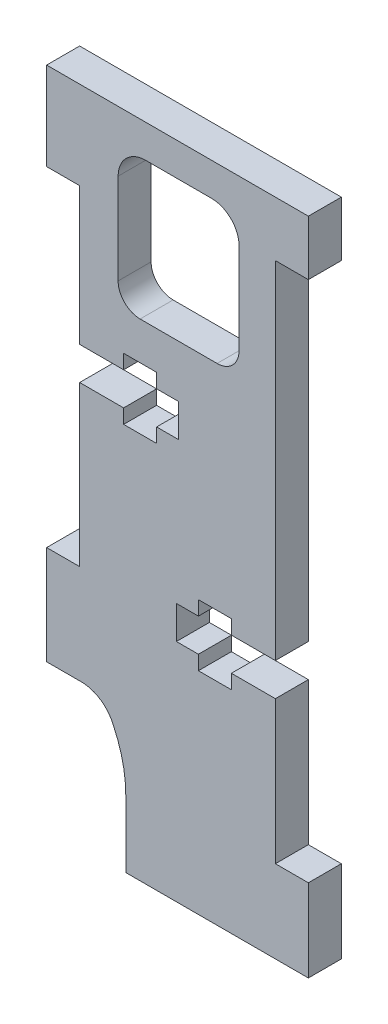
SolidWorks part; units mm, degrees
ref_plane "Front Plane" through (0, 0, 0) normal (0, 0, 1) x (1, 0, 0)
ref_plane "Top Plane" through (0, 0, 0) normal (0, 1, 0) x (1, 0, 0)
ref_plane "Right Plane" through (0, 0, 0) normal (1, 0, 0) x (0, 0, -1)
sketch "Model" plane through (0, 0, 0) normal (0, 0, 1) x (1, 0, 0)
  line L0 (37.008, 72.936) -> (25.508, 72.936)
  line L1 (49.308, 72.936) -> (37.008, 72.936)
  line L2 (49.308, 67.936) -> (49.308, 72.936)
  line L3 (25.508, 30.436) -> (25.508, 34.936)
  line L4 (49.308, 12.936) -> (49.308, 20.436)
  line L5 (32.708, 12.936) -> (49.308, 12.936)
  line L6 (32.708, 18.936) -> (32.708, 12.936)
  line L7 (25.508, 25.936) -> (28.7315, 25.936)
  line L8 (46.308, 20.436) -> (49.308, 20.436)
  line L9 (46.308, 33.436) -> (46.308, 20.436)
  line L10 (42.308, 33.436) -> (46.308, 33.436)
  line L11 (42.308, 32.136) -> (42.308, 33.436)
  line L12 (39.308, 32.136) -> (42.308, 32.136)
  line L13 (39.308, 33.436) -> (39.308, 32.136)
  line L14 (37.308, 33.436) -> (39.308, 33.436)
  line L15 (37.308, 36.436) -> (37.308, 33.436)
  line L16 (39.308, 36.436) -> (37.308, 36.436)
  line L17 (39.308, 37.736) -> (39.308, 36.436)
  line L18 (42.308, 37.736) -> (39.308, 37.736)
  line L19 (42.308, 36.436) -> (42.308, 37.736)
  line L20 (46.308, 36.436) -> (42.308, 36.436)
  line L21 (46.308, 67.936) -> (46.308, 36.436)
  line L22 (49.308, 67.936) -> (46.308, 67.936)
  line L23 (28.508, 64.936) -> (25.508, 64.936)
  line L24 (28.508, 52.436) -> (28.508, 64.936)
  line L25 (32.508, 52.436) -> (28.508, 52.436)
  line L26 (32.508, 53.736) -> (32.508, 52.436)
  line L27 (35.508, 53.736) -> (32.508, 53.736)
  line L28 (35.508, 52.436) -> (35.508, 53.736)
  line L29 (37.508, 52.436) -> (35.508, 52.436)
  line L30 (37.508, 49.436) -> (37.508, 52.436)
  line L31 (35.508, 49.436) -> (37.508, 49.436)
  line L32 (35.508, 48.136) -> (35.508, 49.436)
  line L33 (32.508, 48.136) -> (35.508, 48.136)
  line L34 (32.508, 49.436) -> (32.508, 48.136)
  line L35 (28.508, 49.436) -> (32.508, 49.436)
  line L36 (28.508, 34.936) -> (28.508, 49.436)
  line L37 (25.508, 34.936) -> (28.508, 34.936)
  line L38 (41.008, 57.1861) -> (34.008, 57.1861)
  line L39 (43.008, 67.436) -> (43.008, 59.186)
  line L40 (34.508, 69.936) -> (40.508, 69.936)
  line L41 (32.008, 59.186) -> (32.008, 67.436)
  line L42 (25.508, 30.436) -> (25.508, 25.936)
  line L43 (25.508, 72.936) -> (25.508, 64.936)
  arc A0 (32.708, 18.936) -> (31.569, 23.9827) centre (21.2768, 19.008) ccw
  arc A1 (31.569, 23.9827) -> (28.7315, 25.936) centre (28.6489, 22.7783) ccw
  arc A2 (41.008, 57.1861) -> (43.008, 59.186) centre (41.0081, 59.186) ccw
  arc A3 (43.008, 67.436) -> (40.508, 69.936) centre (40.508, 67.436) ccw
  arc A4 (34.508, 69.936) -> (32.008, 67.436) centre (34.5079, 67.4361) ccw
  arc A5 (32.008, 59.186) -> (34.008, 57.1861) centre (34.0077, 59.1858) ccw
extrude "Boss-Extrude1" add sketch "Model" along normal blind 3
